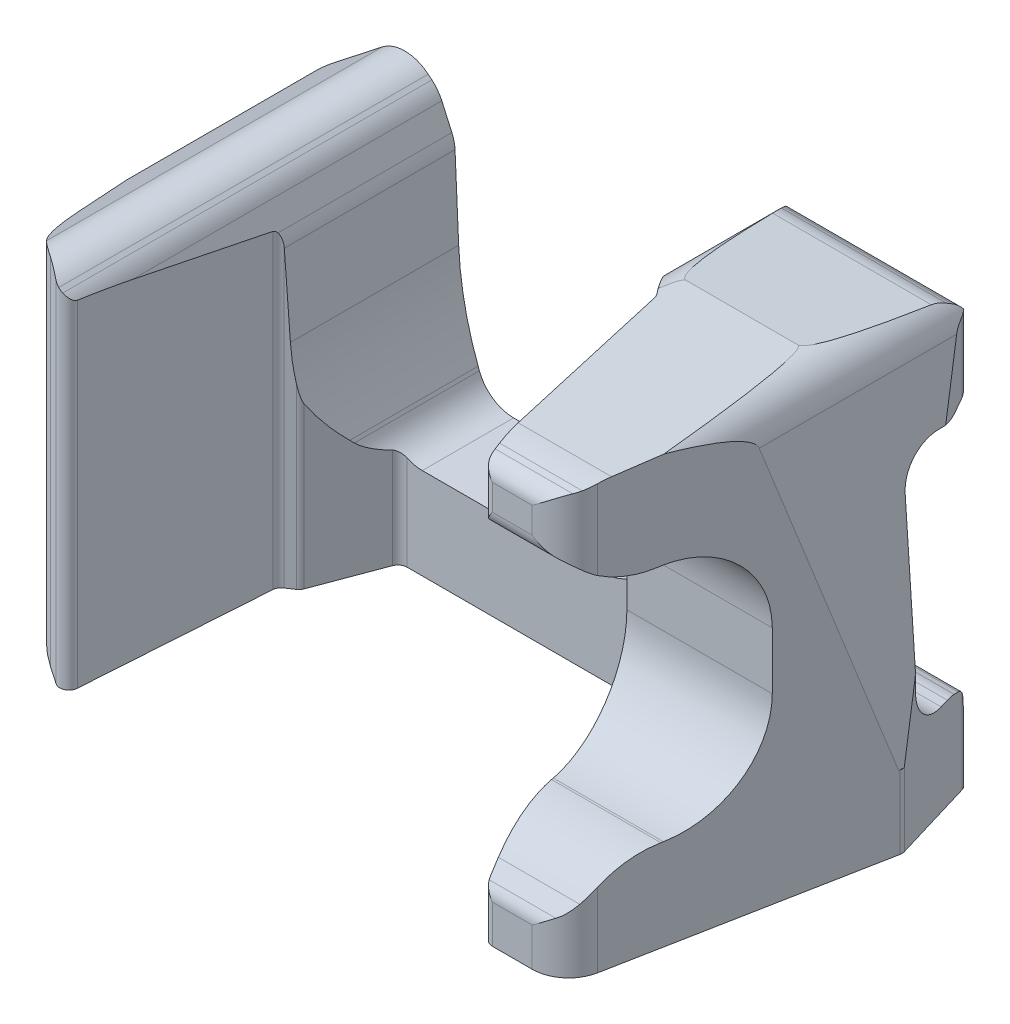
SolidWorks part; units mm, degrees
ref_plane "Front Plane" through (0, 0, 0) normal (0, 0, 1) x (1, 0, 0)
ref_plane "Top Plane" through (0, 0, 0) normal (0, 1, 0) x (1, 0, 0)
ref_plane "Right Plane" through (0, 0, 0) normal (1, 0, 0) x (0, 0, -1)
sketch "Sketch2" plane through (0, 0, 0) normal (0, 1, 0) x (1, 0, 0)
  line L0 (-32.5525, 10) -> (36.1595, 10)
  line L1 (37.1173, 9.2873) -> (39.8331, 0.2348)
  line L2 (39.8573, -0.2408) -> (34.5259, -28.0531)
  line L3 (30.5974, -31.3) -> (26.2288, -31.3)
  line L4 (25.247, -30.4896) -> (20.9472, -8.2261)
  line L5 (20.7653, -7.8158) -> (15.2035, -0.4)
  line L6 (14.4035, 0) -> (-14.4035, 0)
  line L8 (-22.5417, -30.3104) -> (-24.5804, -28.9143)
  line L9 (-31.9133, -18.2634) -> (-36.2335, -0.2623)
  line L10 (-36.219, 0.2584) -> (-33.5103, 9.2873)
  line L11 (-15.3398, -0.6489) -> (-17.9832, -7.698)
  line L12 (-18.3649, -8.1789) -> (-19.1865, -8.7267)
  line L13 (-19.6296, -9.4916) -> (-20.9789, -29.5524)
  arc A0 (-36.219, 0.2584) -> (-36.2335, -0.2623) centre (-35.2612, -0.029) ccw
  arc A1 (39.8331, 0.2348) -> (39.8573, -0.2408) centre (38.8752, -0.0525) cw
  arc A2 (36.1595, 10) -> (37.1173, 9.2873) centre (36.1595, 9) cw
  arc A3 (-33.5103, 9.2873) -> (-32.5525, 10) centre (-32.5525, 9) cw
  arc A4 (26.2288, -31.3) -> (25.247, -30.4896) centre (26.2288, -30.3) cw
  arc A5 (20.7653, -7.8158) -> (20.9472, -8.2261) centre (19.9653, -8.4158) cw
  arc A6 (14.4035, 0) -> (15.2035, -0.4) centre (14.4035, -1) cw
  arc A7 (-15.3398, -0.6489) -> (-14.4035, 0) centre (-14.4035, -1) cw
  arc A8 (-18.3649, -8.1789) -> (-17.9832, -7.698) centre (-18.9196, -7.3469) ccw
  arc A9 (-19.1865, -8.7267) -> (-19.6296, -9.4916) centre (-18.6318, -9.5587) ccw
  arc A10 (-22.5417, -30.3104) -> (-20.9789, -29.5524) centre (-21.9767, -29.4853) ccw
  arc A11 (-31.9133, -18.2634) -> (-24.5804, -28.9143) centre (-14.4103, -14.0627) ccw
  arc A12 (34.5259, -28.0531) -> (30.5974, -31.3) centre (30.5974, -27.3) cw
  point P8 (-28.5867, -24.1749)
  point P13 (0, 0)
  point P14 (12.1787, -0.9186)
  point P15 (21.1337, -1.4532)
  point P16 (0, 0)
  point P17 (-17.3595, -3.0571)
  point P18 (0, 0)
  point P21 (28.0839, -31.3)
  point P22 (21.5347, -7.7351)
  point P23 (-21, -31.3)
  point P24 (-30.2, -23.4845)
  point P25 (-18, -6.8442)
  point P26 (-20.104, -9.1738)
  point P27 (0, 0)
  point P28 (-18, -7.3988)
  point P29 (25.7123, -31.3)
  point P30 (-19.6603, -9)
  point P31 (-21, -31.3)
  point P32 (0, 0)
  point P33 (-30.2, -25.0376)
  point P36 (-36.2965, 0)
  point P39 (39.9035, 0)
  point P42 (36.9035, 10)
  point P45 (-33.2965, 10)
  point P48 (25.4035, -31.3)
  point P51 (20.9035, -8)
  point P54 (14.9035, 0)
  point P57 (-15.0965, 0)
  point P60 (-18.0965, -8)
  point P63 (-19.5965, -9)
  point P66 (-21.0965, -31.3)
  point P69 (-30.2965, -25)
  point P72 (33.9035, -31.3)
  dimension "D18" = 1
  dimension "D19" = 18
  dimension "D20" = 4
  dimension "D1" = 41.3
  dimension "D2" = 76.2
  dimension "D3" = 10
  dimension "D4" = 30
  dimension "D5" = 3
  dimension "D6" = 3
  dimension "D7" = 25
  dimension "D8" = 6
  dimension "D9" = 6
  dimension "D10" = 6
  dimension "D11" = 3
  dimension "D12" = 3
  dimension "D13" = 8
  dimension "D14" = 1
  dimension "D15" = 8.5
  dimension "D16" = 1.5
  dimension "D17" = 25
extrude "Boss-Extrude1" add sketch "Sketch2" along normal blind 47.5 contours L0 A2 L1 A1 L2 A12 L3 A4 L4 A5 L5 A6 L6 A7 L11 A8 L12 A9 L13 A10 L8 A11 L9 A0 L10 A3
sketch "Sketch3" plane through (0, 0, -10) normal (0, 0, -1) x (-1, 0, 0)
  line L0 (-39.8331, 8) -> (-37.3734, 43.7744)
  line L1 (-39.8331, 8) -> (-40.7232, 8)
  line L2 (-39.8331, 47.5) -> (-39.8331, 0) construction
  line L3 (-33.3829, 47.5) -> (-21.1681, 47.5)
  line L4 (32.5525, 47.5) -> (-36.1595, 47.5) construction
  line L5 (-17.1684, 43.4495) -> (-17.4099, 24.3239)
  line L6 (-13.0177, 13.528) -> (-12.1257, 12.636)
  line L7 (-5.7618, 10) -> (12.7383, 10)
  line L8 (16.4836, 12.5955) -> (16.6222, 12.965)
  line L9 (18.7525, 23.3719) -> (19.1522, 32.2393)
  line L10 (19.4979, 33.6949) -> (20.6003, 36.155)
  line L11 (21.6904, 37.5927) -> (22.0967, 37.931)
  line L12 (-40.7232, 48.3251) -> (36.8218, 48.3251)
  line L13 (27.1245, 38.0057) -> (33.5103, 33)
  line L14 (33.5103, 33) -> (36.219, 8)
  line L15 (36.219, 47.5) -> (36.219, 0) construction
  line L16 (36.219, 8) -> (36.8218, 8)
  line L18 (-21.1681, 47.5) -> (-33.3829, 47.5)
  line L20 (33.5103, 47.5) -> (33.5103, 0) construction
  line L21 (36.8218, 8) -> (36.8218, 48.3251)
  line L22 (-40.7232, 8) -> (-40.7232, 48.3251)
  line L24 (32.5525, 0) -> (-36.1595, 0) construction
  arc A0 (21.6904, 37.5927) -> (20.6003, 36.155) centre (24.2506, 34.5193) ccw
  arc A1 (19.4979, 33.6949) -> (19.1522, 32.2393) centre (23.1482, 32.0592) ccw
  arc A2 (-21.1681, 47.5) -> (-17.1684, 43.4495) centre (-21.1681, 43.5) cw
  arc A3 (22.0967, 37.931) -> (27.1245, 38.0057) centre (24.6568, 34.8577) cw
  arc A4 (-33.3829, 47.5) -> (-37.3734, 43.7744) centre (-33.3829, 43.5) ccw
  arc A5 (16.6222, 12.965) -> (18.7525, 23.3719) centre (-15.213, 24.9032) ccw
  arc A6 (12.7383, 10) -> (16.4836, 12.5955) centre (12.7383, 14) ccw
  arc A7 (-12.1257, 12.636) -> (-5.7618, 10) centre (-5.7618, 19) ccw
  arc A8 (-17.4099, 24.3239) -> (-13.0177, 13.528) centre (-2.4111, 24.1346) ccw
  point P20 (0, 0)
  point P21 (0, 0)
  point P24 (0, 0)
  point P71 (20.9789, 37)
  point P74 (19.1865, 33)
  point P77 (-17.1173, 47.5)
  point P80 (24.5804, 40)
  point P83 (-37.1173, 47.5)
  point P86 (18.5103, 18)
  point P89 (15.5103, 10)
  point P92 (-9.4897, 10)
  point P95 (-17.4897, 18)
  dimension "D12" = 4
  dimension "D13" = 34
  dimension "D14" = 4
  dimension "D15" = 9
  dimension "D16" = 15
  dimension "D1" = 10
  dimension "D2" = 25
  dimension "D3" = 40
  dimension "D4" = 15
  dimension "D5" = 3
  dimension "D6" = 8
  dimension "D7" = 20
  dimension "D8" = 8
  dimension "D9" = 8
  dimension "D10" = 15
  dimension "D11" = 3
extrude "Cut-Extrude1" cut sketch "Sketch3" against normal up to surface (41.3 mm away)
sketch "Sketch4" plane through (0, 0, 0) normal (1, 0, 0) x (0, 0, -1)
  line L1 (-31.3, 47.5) -> (-31.3, 0) construction
  line L2 (-12, 20) -> (-12, 26.2507)
  line L5 (-29.4517, 6.9253) -> (-30.7428, 5.5804)
  line L7 (-5, 47.5) -> (-32.3, 47.5)
  line L10 (-22.2378, 10) -> (-22, 10)
  line L12 (-22, 36.2507) -> (-22.8795, 36.2507)
  line L13 (-29.2813, 38.5685) -> (-30.5804, 39.651)
  line L14 (-0.2408, 0) -> (-28.0531, 0) construction
  line L16 (-5, 47.5) -> (-26.7702, 46.5556)
  line L17 (-29.2802, 46.1221) -> (-29.8887, 45.9347)
  line L19 (-30.1708, 47.5) -> (10, 47.5) construction
  line L20 (-28.0531, 47.3332) -> (-28.0531, 0) construction
  line L21 (-31.3, 41.1875) -> (-31.3, 44.0233)
  line L22 (-31.3, 4.1954) -> (-31.3, 0)
  line L23 (-31.3, 0) -> (-28.0531, 0) construction
  line L24 (-31.3, 0) -> (-32.3, 0)
  line L25 (-32.3, 0) -> (-32.3, 47.5)
  line L26 (11, 47.5) -> (11, 0)
  line L27 (11, 0) -> (10, 0)
  line L28 (10, 0) -> (10, 4.6074)
  line L29 (10, 46.3793) -> (10, 0) construction
  line L31 (6.98, 10) -> (6, 10)
  line L32 (2, 14) -> (2, 32.2507)
  line L33 (6, 36.2507) -> (7.169, 36.2507)
  line L34 (8.2327, 36.557) -> (9.0637, 37.079)
  line L35 (10, 38.7726) -> (10, 44.1991)
  line L36 (8.8108, 46.0274) -> (8.3709, 46.2224)
  line L37 (7.0623, 46.5536) -> (-5, 47.5)
  line L38 (-5, 47.5) -> (11, 47.5)
  line L39 (8.0517, 9.8538) -> (8.6679, 9.6824)
  line L40 (9.2873, 44.9332) -> (9.2873, 0) construction
  line L41 (9.3877, 8.875) -> (9.9387, 5.3878)
  arc A0 (-29.4517, 6.9253) -> (-22.2378, 10) centre (-22.2378, 0) cw
  arc A1 (-22, 10) -> (-12, 20) centre (-22, 20) ccw
  arc A2 (-12, 26.2507) -> (-22, 36.2507) centre (-22, 26.2507) ccw
  arc A3 (-26.7702, 46.5556) -> (-29.2802, 46.1221) centre (-26.3368, 36.565) ccw
  arc A4 (-22.8795, 36.2507) -> (-29.2813, 38.5685) centre (-22.8795, 46.2507) cw
  arc A5 (-31.3, 44.0233) -> (-29.8887, 45.9347) centre (-29.3, 44.0233) cw
  arc A6 (-31.3, 41.1875) -> (-30.5804, 39.651) centre (-29.3, 41.1875) ccw
  arc A7 (-31.3, 4.1954) -> (-30.7428, 5.5804) centre (-29.3, 4.1954) cw
  arc A8 (7.0623, 46.5536) -> (8.3709, 46.2224) centre (6.7494, 42.5658) cw
  arc A9 (6, 10) -> (2, 14) centre (6, 14) cw
  arc A10 (2, 32.2507) -> (6, 36.2507) centre (6, 32.2507) cw
  arc A11 (7.169, 36.2507) -> (8.2327, 36.557) centre (7.169, 38.2507) ccw
  arc A12 (9.0637, 37.079) -> (10, 38.7726) centre (8, 38.7726) ccw
  arc A13 (8.8108, 46.0274) -> (10, 44.1991) centre (8, 44.1991) cw
  arc A14 (6.98, 10) -> (8.0517, 9.8538) centre (6.98, 6) cw
  arc A15 (8.6679, 9.6824) -> (9.3877, 8.875) centre (8.4, 8.719) cw
  arc A16 (10, 4.6074) -> (9.9387, 5.3878) centre (5, 4.6074) ccw
  point P36 (-26.5, 10)
  point P43 (-28.0531, 46.5)
  point P48 (-31.3, 45.5)
  point P51 (-31.3, 40.2507)
  point P54 (-31.3, 5)
  point P58 (0, 0)
  point P62 (-22.4398, 36.2507)
  point P67 (9.2873, 9.5101)
  point P71 (10, 5)
  point P74 (7.7449, 46.5)
  point P81 (7.7449, 36.2507)
  point P84 (10, 37.667)
  point P87 (10, 45.5)
  point P88 (0, 0)
  point P89 (0, 0)
  point P92 (0, 0)
  point P93 (0, 0)
  point P94 (0, 0)
  point P95 (0, 0)
  point P96 (0, 0)
  point P97 (0, 0)
  point P98 (8.2553, 36.5997)
  point P99 (9.0441, 37.0459)
  point P100 (8.2327, 36.565)
  point P101 (0, 0)
  point P102 (0, 0)
  point P103 (0, 0)
  point P104 (0, 0)
  dimension "D15" = 10
  dimension "D6" = 2
  dimension "D16" = 4
  dimension "D17" = 2
  dimension "D18" = 2
  dimension "D19" = 4
  dimension "D20" = 1
  dimension "D21" = 5
  dimension "D2" = 5
  dimension "D3" = 10
  dimension "D4" = 4
  dimension "D5" = 2
  dimension "D7" = 14
  dimension "D8" = 5
  dimension "D9" = 2
  dimension "D10" = 1
  dimension "D11" = 1
  dimension "D12" = 7
  dimension "D13" = 12
  dimension "D14" = 1
  dimension "D22" = 1
extrude "Cut-Extrude2" cut sketch "Sketch4" along normal blind 40.5 contours L22 A7 L5 A0 L10 A1 L2 A2 L12 A4 L13 A6 L21 A5 L17 A3 L16 L7 L25 L24 | A16 L28 L27 L26 L38 L37 A8 L36 A13 L35 A12 L34 A11 L33 A10 L32 A9 L31 A14 L39 A15 L41
